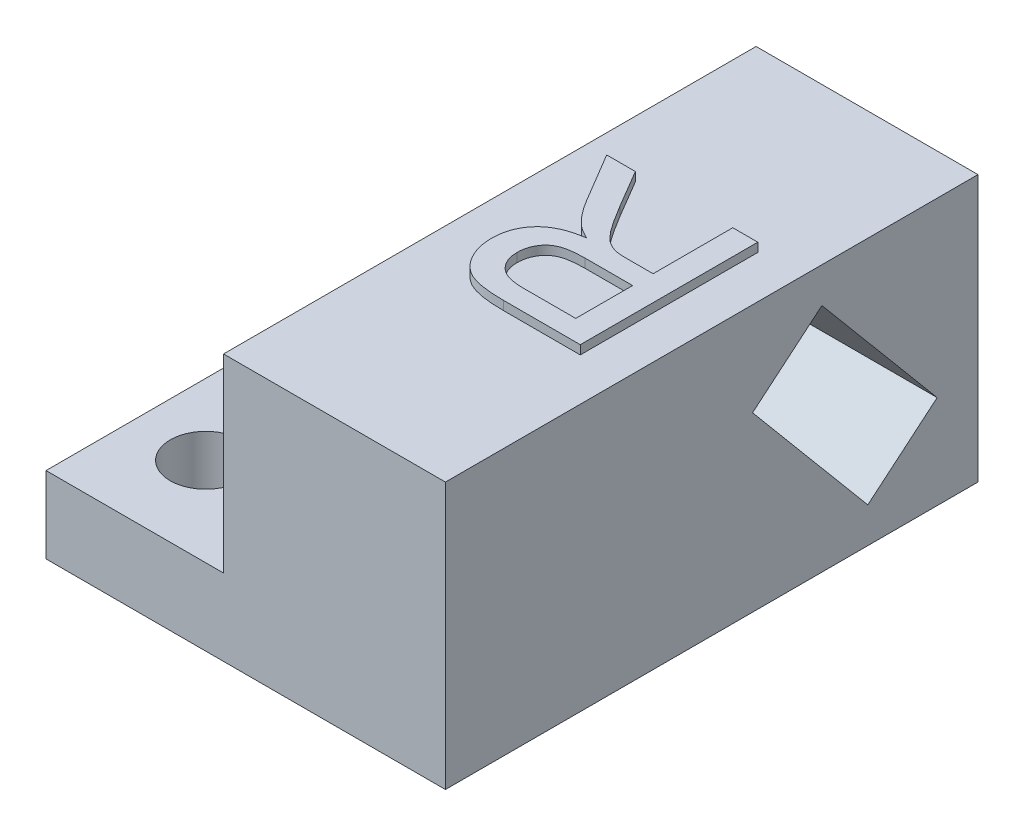
SolidWorks part; units mm, degrees
ref_plane "Спереди" through (0, 0, 0) normal (0, 0, 1) x (1, 0, 0)
ref_plane "Сверху" through (0, 0, 0) normal (0, 1, 0) x (1, 0, 0)
ref_plane "Справа" through (0, 0, 0) normal (1, 0, 0) x (0, 0, -1)
sketch "Sketch1" plane through (0, 0, 0) normal (0, 1, 0) x (1, 0, 0)
  line L1 (12.5, -30) -> (-12.5, -30)
  line L2 (12.5, -30) -> (12.5, 30)
  line L3 (12.5, 30) -> (-12.5, 30)
  line L4 (-12.5, -30) -> (-12.5, 30)
  line L5 (12.5, -30) -> (-12.5, 30) construction
  line L6 (12.5, 30) -> (-12.5, -30) construction
  point P0 (0, 0)
  dimension "D1" = 25
  dimension "D2" = 60
extrude "Boss-Extrude1" add sketch "Sketch1" along normal blind 30
sketch "Sketch2" plane through (-12.5, 0, 0) normal (-1, 0, 0) x (0, 0, 1)
  line L0 (-30, 4.3119) -> (30, 4.3119) construction
  line L1 (-30, 30) -> (-30, 0) construction
  line L2 (30, 30) -> (30, 0) construction
  line L4 (30, 8.6238) -> (-30, 8.6238)
  line L5 (30, 8.6238) -> (30, 0)
  line L6 (30, 0) -> (-30, 0)
  line L7 (-30, 8.6238) -> (-30, 0)
  line L8 (30, 8.6238) -> (-30, 0) construction
  line L9 (30, 0) -> (-30, 8.6238) construction
  point P6 (0, 4.3119)
extrude "Boss-Extrude2" add sketch "Sketch2" along normal blind 20
sketch "Sketch3" plane through (0, 8.6238, 0) normal (0, 1, 0) x (1, 0, 0)
  line L0 (-24.5, -30) -> (-24.5, 30) construction
  line L1 (-32.5, 30) -> (-12.5, 30) construction
  line L2 (-32.5, -30) -> (-12.5, -30) construction
  circle A0 centre (-24.5, 20) radius 4
  circle A1 centre (-24.5, -20) radius 4
  dimension "D1" = 8
  dimension "D2" = 8
  dimension "D3" = 10
  dimension "D4" = 10
extrude "Cut-Extrude1" cut sketch "Sketch3" against normal through all
sketch "Sketch4" plane through (12.5, 0, 0) normal (1, 0, 0) x (0, 0, -1)
  line L0 (15, 30) -> (15, 0) construction
  line L1 (12.4147, 26.0153) -> (25.399, 10.5412)
  line L2 (12.4147, 26.0153) -> (4.601, 19.4588)
  line L3 (-30, 30) -> (30, 30) construction
  line L4 (20.1, 4.9) -> (9.9, 4.9) construction
  line L5 (20.1, 4.9) -> (20.1, 25.1) construction
  line L6 (20.1, 25.1) -> (9.9, 25.1) construction
  line L7 (9.9, 4.9) -> (9.9, 25.1) construction
  line L8 (20.1, 4.9) -> (9.9, 25.1) construction
  line L9 (20.1, 25.1) -> (9.9, 4.9) construction
  line L10 (-30, 0) -> (30, 0) construction
  line L11 (30, 30) -> (30, 0) construction
  line L12 (25.399, 10.5412) -> (17.5853, 3.9847)
  line L13 (4.601, 19.4588) -> (17.5853, 3.9847)
  line L14 (21.4922, 7.263) -> (8.5078, 22.737) construction
  line L15 (18.9068, 18.2782) -> (11.0932, 11.7218) construction
  point P6 (15, 15)
  point P12 (15, 15)
  point P13 (15, 15)
  dimension "D1" = 20.2
  dimension "D2" = 10.2
  dimension "D3" = 15
  dimension "D4" = 20.2
  dimension "D5" = 10.2
  dimension "D6" = 40
extrude "Cut-Extrude2" cut sketch "Sketch4" against normal blind 20
sketch "Sketch5" plane through (0, 30, 0) normal (0, 1, 0) x (1, 0, 0)
  line L0 (12.5, 10) -> (-12.5, 10) construction
  line L1 (12.5, -30) -> (12.5, 30) construction
  line L2 (-12.5, 30) -> (-12.5, -30) construction
  line L3 (12.5, 30) -> (-12.5, 30) construction
  text T0 "R" font "Arial" height 20
  dimension "D1" = 20
extrude "Boss-Extrude3" add sketch "Sketch5" along normal blind 1
